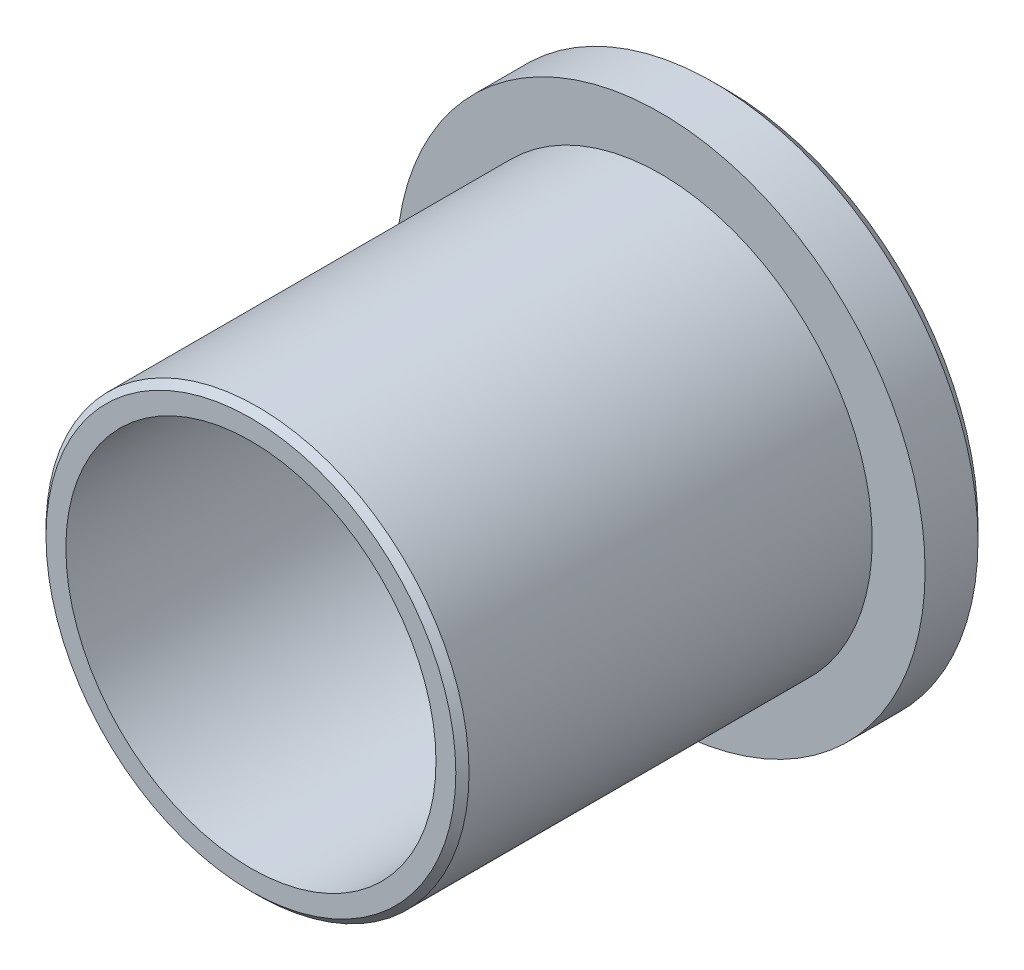
SolidWorks part; units mm, degrees
ref_plane "Front Plane" through (0, 0, 0) normal (0, 0, 1) x (1, 0, 0)
ref_plane "Top Plane" through (0, 0, 0) normal (0, 1, 0) x (1, 0, 0)
ref_plane "Right Plane" through (0, 0, 0) normal (1, 0, 0) x (0, 0, -1)
sketch "Sketch1" plane through (0, 0, 0) normal (1, 0, 0) x (0, 0, -1)
  line L0 (0, 0) -> (18, 0) construction
  line L1 (0, 7) -> (18, 7)
  line L2 (18, 7) -> (18, 9.5)
  line L3 (17.5, 10) -> (15.5, 10)
  line L4 (15.5, 10) -> (15.5, 8)
  line L5 (15.5, 8) -> (0.25, 8)
  line L6 (0, 7.75) -> (0, 7)
  line L7 (0.25, 8) -> (0, 7.75)
  line L8 (18, 9.5) -> (17.5, 10)
  point P6 (18, 10)
  point P9 (0, 8)
  dimension "D1" = 18
  dimension "D2" = 7
  dimension "D3" = 8
  dimension "D4" = 2
  dimension "D5" = 2.5
revolve "Revolve1" add sketch "Sketch1" angle 360 about L0
sketch "Sketch2" [suppressed] plane through (0, 0, 0) normal (0, 1, 0) x (1, 0, 0)
  circle A0 centre (0, 9.5) radius 1.5
  dimension "D1" = 3
  dimension "D2" = 9.5
extrude "Cut-Extrude2" [suppressed] cut sketch "Sketch2" along normal through all
